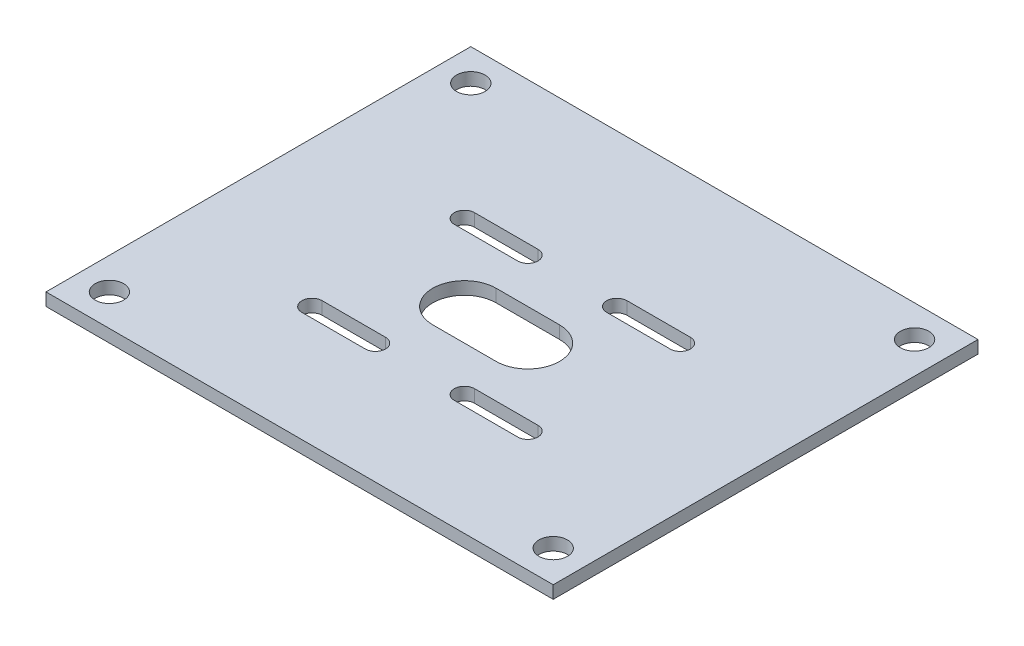
SolidWorks part; units mm, degrees
ref_plane "Front Plane" through (0, 0, 0) normal (0, 0, 1) x (1, 0, 0)
ref_plane "Top Plane" through (0, 0, 0) normal (0, 1, 0) x (1, 0, 0)
ref_plane "Right Plane" through (0, 0, 0) normal (1, 0, 0) x (0, 0, -1)
sketch "Sketch1" plane through (0, 0, 0) normal (0, 1, 0) x (1, 0, 0)
  line L0 (-22.0208, 12.0208) -> (-12.0208, 12.0208) construction
  line L3 (-40, -26) -> (30, -26) construction
  line L5 (-15, 15) -> (15, 15) construction
  line L6 (-15, 15) -> (-15, -15) construction
  line L11 (-15, -15) -> (15, -15) construction
  line L12 (15, 15) -> (15, -15) construction
  line L13 (-15, 15) -> (15, -15) construction
  line L14 (-15, -15) -> (15, 15) construction
  line L15 (-22.0208, 13.6208) -> (-12.0208, 13.6208)
  line L16 (-22.0208, 10.4208) -> (-12.0208, 10.4208)
  line L17 (2.0208, 12.0208) -> (12.0208, 12.0208) construction
  line L18 (2.0208, 13.6208) -> (12.0208, 13.6208)
  line L19 (2.0208, 10.4208) -> (12.0208, 10.4208)
  line L20 (0, 0) -> (17, 0) construction
  line L21 (-10, 0) -> (0, 0) construction
  line L22 (-10, 5) -> (0, 5)
  line L23 (-10, -5) -> (0, -5)
  line L24 (-22.0208, -12.0208) -> (-12.0208, -12.0208) construction
  line L25 (-22.0208, -13.6208) -> (-12.0208, -13.6208)
  line L26 (-22.0208, -10.4208) -> (-12.0208, -10.4208)
  line L27 (2.0208, -12.0208) -> (12.0208, -12.0208) construction
  line L28 (2.0208, -13.6208) -> (12.0208, -13.6208)
  line L29 (2.0208, -10.4208) -> (12.0208, -10.4208)
  line L30 (-40, 31) -> (30, 31) construction
  line L31 (30, 31) -> (30, -26) construction
  line L32 (-40, 31) -> (-40, -26) construction
  line L33 (-45, 36) -> (35, 36)
  line L34 (35, 36) -> (35, -31)
  line L35 (35, -31) -> (-45, -31)
  line L36 (-45, -31) -> (-45, 36)
  circle A0 centre (0, 0) radius 5 construction
  circle A1 centre (0, 0) radius 17 construction
  circle A2 centre (-12.0208, 12.0208) radius 1.6 construction
  circle A3 centre (12.0208, 12.0208) radius 1.6 construction
  arc A4 (-22.0208, 13.6208) -> (-22.0208, 10.4208) centre (-22.0208, 12.0208) ccw
  arc A5 (-12.0208, 10.4208) -> (-12.0208, 13.6208) centre (-12.0208, 12.0208) ccw
  arc A6 (2.0208, 13.6208) -> (2.0208, 10.4208) centre (2.0208, 12.0208) ccw
  arc A7 (12.0208, 10.4208) -> (12.0208, 13.6208) centre (12.0208, 12.0208) ccw
  arc A8 (-10, 5) -> (-10, -5) centre (-10, 0) ccw
  arc A9 (0, -5) -> (0, 5) centre (0, 0) ccw
  arc A10 (-22.0208, -13.6208) -> (-22.0208, -10.4208) centre (-22.0208, -12.0208) cw
  arc A11 (-12.0208, -10.4208) -> (-12.0208, -13.6208) centre (-12.0208, -12.0208) cw
  arc A12 (2.0208, -13.6208) -> (2.0208, -10.4208) centre (2.0208, -12.0208) cw
  arc A13 (12.0208, -10.4208) -> (12.0208, -13.6208) centre (12.0208, -12.0208) cw
  circle A16 centre (30, -26) radius 2.25
  circle A17 centre (-40, -26) radius 2.25
  circle A18 centre (-40, 31) radius 2.25
  circle A19 centre (30, 31) radius 2.25
  point P0 (0, 0)
  point P2 (0, 31)
  point P6 (0, 0)
  point P9 (-45, 31)
  point P10 (-40, 36)
  point P11 (0, 0)
  point P23 (-22.0208, 12.0208)
  point P25 (-17.0208, 12.0208)
  point P30 (2.0208, 12.0208)
  point P32 (7.0208, 12.0208)
  point P37 (-10, 0)
  point P40 (-5, 0)
  point P47 (-17.0208, -12.0208)
  point P54 (7.0208, -12.0208)
  point P59 (40, 38.4573)
  point P60 (35, 31)
  point P63 (-40, -31)
  dimension "D7" = 10
  dimension "D9" = 1.6
  dimension "D10" = 1.6
  dimension "D12" = 5
  dimension "D13" = 5
  dimension "D3" = 5
  dimension "D2" = 31
  dimension "D4" = 5
  dimension "D5" = 30
  dimension "D6" = 30
  dimension "D8" = 10
  dimension "D11" = 10
  dimension "D14" = 5
  dimension "D15" = 30
  dimension "D16" = 40
  dimension "D17" = 57
extrude "Boss-Extrude1" add sketch "Sketch1" along normal blind 2
